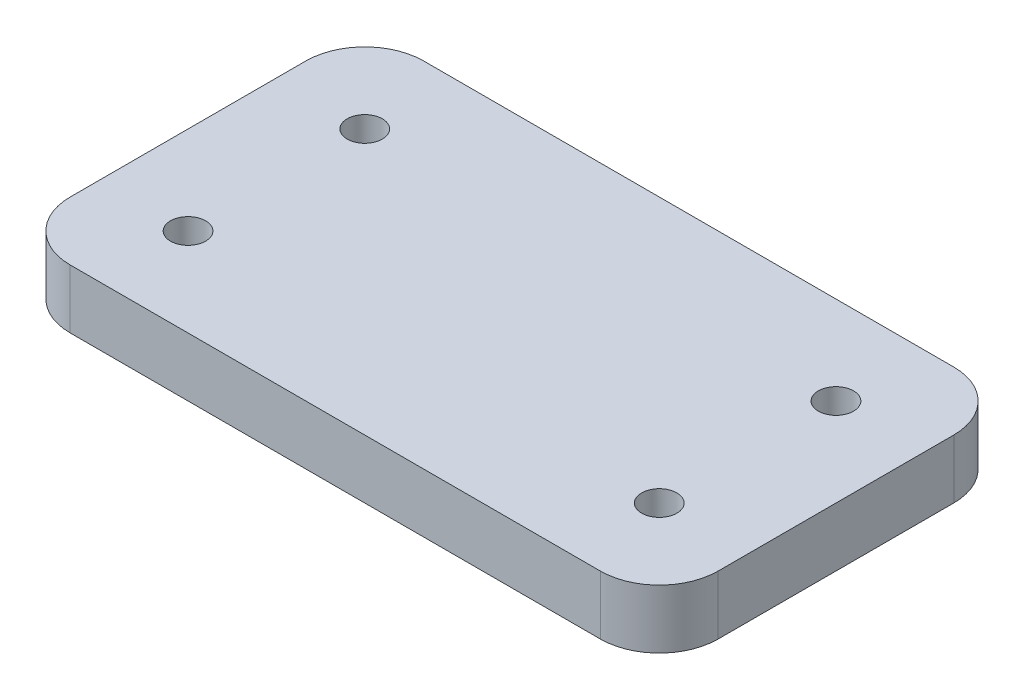
SolidWorks part; units mm, degrees
material "6061-T6 (SS)"
ref_plane "Front Plane" through (0, 0, 0) normal (0, 0, 1) x (1, 0, 0)
ref_plane "Top Plane" through (0, 0, 0) normal (0, 1, 0) x (1, 0, 0)
ref_plane "Right Plane" through (0, 0, 0) normal (1, 0, 0) x (0, 0, -1)
sketch "Sketch1" plane through (0, 0, 0) normal (0, 1, 0) x (1, 0, 0)
  line L1 (34.925, 19.05) -> (-34.925, 19.05)
  line L2 (34.925, 19.05) -> (34.925, -19.05)
  line L3 (34.925, -19.05) -> (-34.925, -19.05)
  line L4 (-34.925, 19.05) -> (-34.925, -19.05)
  line L5 (34.925, 19.05) -> (-34.925, -19.05) construction
  line L6 (34.925, -19.05) -> (-34.925, 19.05) construction
  point P0 (0, 0)
  dimension "D1" = 69.85
  dimension "D2" = 38.1
extrude "Boss-Extrude1" add sketch "Sketch1" along normal blind 6.35
hole_wizard "#6 Clearance Hole1" positions "Sketch3" profile "Sketch2" hole size "#6" standard "Ansi Inch"
sketch "Sketch3" plane through (0, 0, 0) normal (0, 1, 0) x (1, 0, 0)
  line L1 (25.4, 9.525) -> (-25.4, 9.525)
  line L2 (25.4, 9.525) -> (25.4, -9.525)
  line L3 (25.4, -9.525) -> (-25.4, -9.525)
  line L4 (-25.4, 9.525) -> (-25.4, -9.525)
  line L5 (25.4, 9.525) -> (-25.4, -9.525) construction
  line L6 (25.4, -9.525) -> (-25.4, 9.525) construction
  point P0 (-25.4, -9.525)
  point P1 (25.4, 9.525)
  point P3 (-25.4, 9.525)
  point P5 (25.4, -9.525)
  dimension "D1" = 19.05
  dimension "D2" = 50.8
sketch "Sketch2" plane through (-25.4, 0, 9.525) normal (1, 0, 0) x (0, 0, -1)
  line L0 (0, 0) -> (0, 26.5408)
  line L1 (0, 26.5408) -> (1.8986, 25.4)
  line L2 (1.8986, 25.4) -> (1.8986, 0)
  line L5 (1.8986, 0) -> (0, 0)
  line L10 (0, 26.5408) -> (-1.8986, 25.4) construction
  line L11 (0, -6.35) -> (0, 107.95) construction
  dimension "Hole Dia." = 3.7973
  dimension "Hole Depth" = 25.4
  dimension "Drill Angle" = 118
fillet "Fillet1" radius 6.35 4 edges at (-34.925, 3.175, -19.05) (-34.925, 3.175, 19.05) (34.925, 3.175, 19.05) (34.925, 3.175, -19.05)
